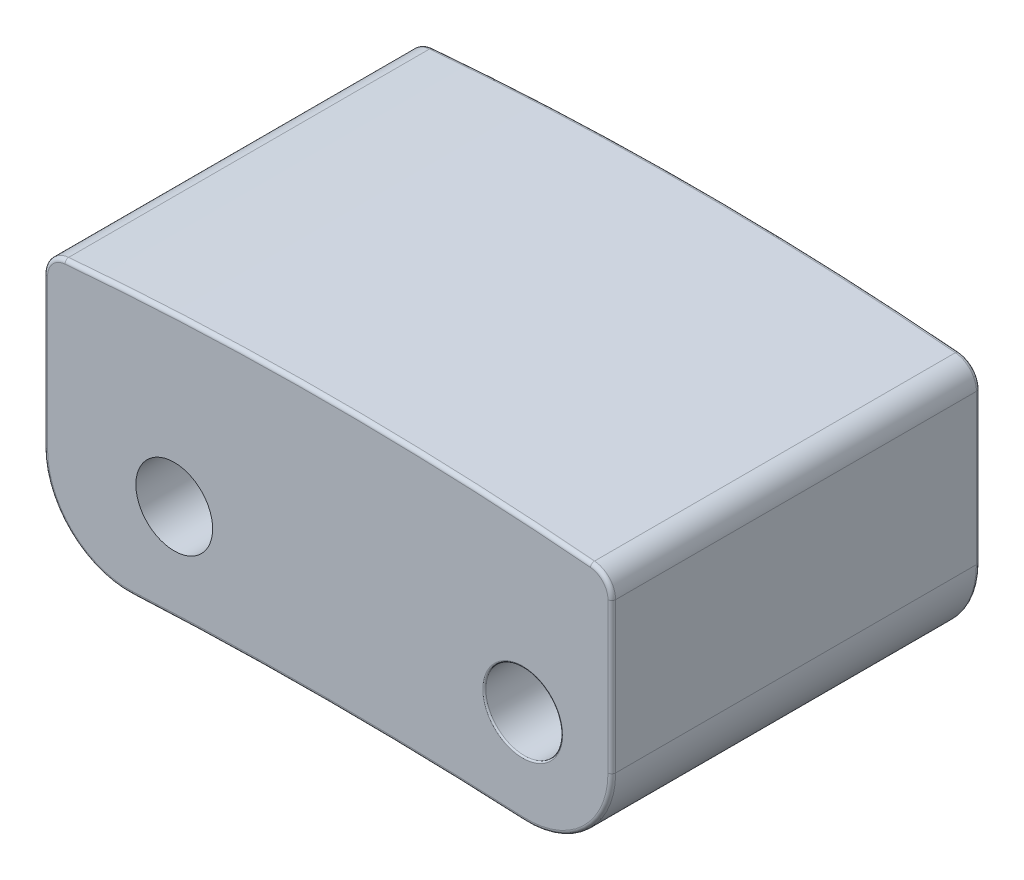
SolidWorks part; units mm, degrees
ref_plane "Front Plane" through (0, 0, 0) normal (0, 0, 1) x (1, 0, 0)
ref_plane "Top Plane" through (0, 0, 0) normal (0, 1, 0) x (1, 0, 0)
ref_plane "Right Plane" through (0, 0, 0) normal (1, 0, 0) x (0, 0, -1)
sketch "Sketch1" plane through (0, 0, 0) normal (0, 0, 1) x (1, 0, 0)
  line L0 (55, 0) -> (-55, 0) construction
  line L1 (-3.7, 1.85) -> (3.7, 1.85)
  line L2 (-3.7, 1.85) -> (-3.7, -1.85)
  line L3 (-3.7, -1.85) -> (3.7, -1.85)
  line L4 (3.7, 1.85) -> (3.7, -1.85)
  line L5 (0, -55) -> (0, 55) construction
  dimension "D1" = 7.4
  dimension "D2" = 3.7
  dimension "D3" = 1.85
  dimension "D4" = 3.7
extrude "Boss-Extrude1" add sketch "Sketch1" along normal mid plane 4.8
sketch "Sketch2" plane through (0, 0, 2.4) normal (0, 0, 1) x (1, 0, 0)
  line L0 (-3.7, 1.85) -> (-3.7, -1.85) construction
  line L1 (3.7, -1.85) -> (3.7, 1.85) construction
  line L2 (-3.7, -1.85) -> (3.7, -1.85) construction
  line L3 (3.7, 1.85) -> (-3.7, 1.85) construction
  line L4 (-3.7, 1.55) -> (-7.1207, 4.0114)
  line L5 (-7.1207, 4.0114) -> (5.5359, 3.8867)
  line L6 (5.5359, 3.8867) -> (3.7, 1.55)
  line L7 (3.7, -1.85) -> (0.3506, -3.782)
  line L8 (-3.7, -1.85) -> (0.3506, -3.782)
  arc A0 (-3.7, 1.55) -> (3.7, 1.55) centre (0, -38.2785) cw
  arc A1 (-3.7, -1.85) -> (3.7, -1.85) centre (0, -51.7129) cw
  dimension "D4" = 40
  dimension "D5" = 50
  dimension "D1" = 0
  dimension "D2" = 0.3
  dimension "D3" = 0.3
extrude "Cut-Extrude1" cut sketch "Sketch2" against normal blind 4.8
fillet "Fillet1" radius 1.1 2 edges at (3.7, -1.85, 0) (-3.7, -1.85, 0)
fillet "Fillet2" radius 0.3 2 edges at (3.7, 1.55, 0) (-3.7, 1.55, 0)
fillet "Fillet3" radius 0.05 16 edges at (-3.621, 1.4785, -2.4) (-3.7, 0.2983, -2.4) (-3.3578, -1.4765, -2.4) (0, -1.7129, -2.4) (3.3578, -1.4765, -2.4) (3.7, 0.2983, -2.4) (3.621, 1.4785, -2.4) (0, 1.7215, -2.4) (3.3578, -1.4765, 2.4) (0, -1.7129, 2.4) (-3.3578, -1.4765, 2.4) (-3.7, 0.2983, 2.4) (-3.621, 1.4785, 2.4) (0, 1.7215, 2.4) (3.621, 1.4785, 2.4) (3.7, 0.2983, 2.4)
sketch "Sketch3" plane through (0, 0, 2.4) normal (0, 0, 1) x (1, 0, 0)
  circle A0 centre (2.5394, -0.5484) radius 0.5
  dimension "D1" = 1
extrude "Cut-Extrude2" cut sketch "Sketch3" against normal mid plane 14.8 from offset 1 offset against normal yes
fillet "Fillet4" radius 0.02 2 edges at (3.0394, -0.5484, -2.4) (3.0394, -0.5484, 2.4)
sketch "Sketch4" plane through (0, 0, -2.4) normal (0, 0, -1) x (-1, 0, 0)
  line L0 (2.64, 0) -> (-2.64, 0) construction
  line L1 (0, 1.9253) -> (0, -1.9253) construction
  circle A0 centre (2, -0.5) radius 0.5
  dimension "D1" = 1
  dimension "D2" = 0.5
  dimension "D3" = 2
extrude "Cut-Extrude3" cut sketch "Sketch4" against normal blind 4.5 from offset 1 offset against normal yes
sketch "Sketch5" plane through (0, 0, 0) normal (0, 1, 0) x (1, 0, 0)
  line L0 (-2.5466, -2.4) -> (2.5466, -2.4) construction
  line L2 (3.7, 2.35) -> (3.7, -2.35) construction
  circle A0 centre (0.7, -1) radius 0.4
  dimension "D1" = 0.8
  dimension "D2" = 1.4
  dimension "D3" = 3
extrude "Cut-Extrude4" cut sketch "Sketch5" along normal offset from surface (8.6822 mm away) 0.4 from offset 10 offset against normal yes
fillet "Fillet5" radius 0.05 1 edges at (0.608, -1.7166, 1.3893)
